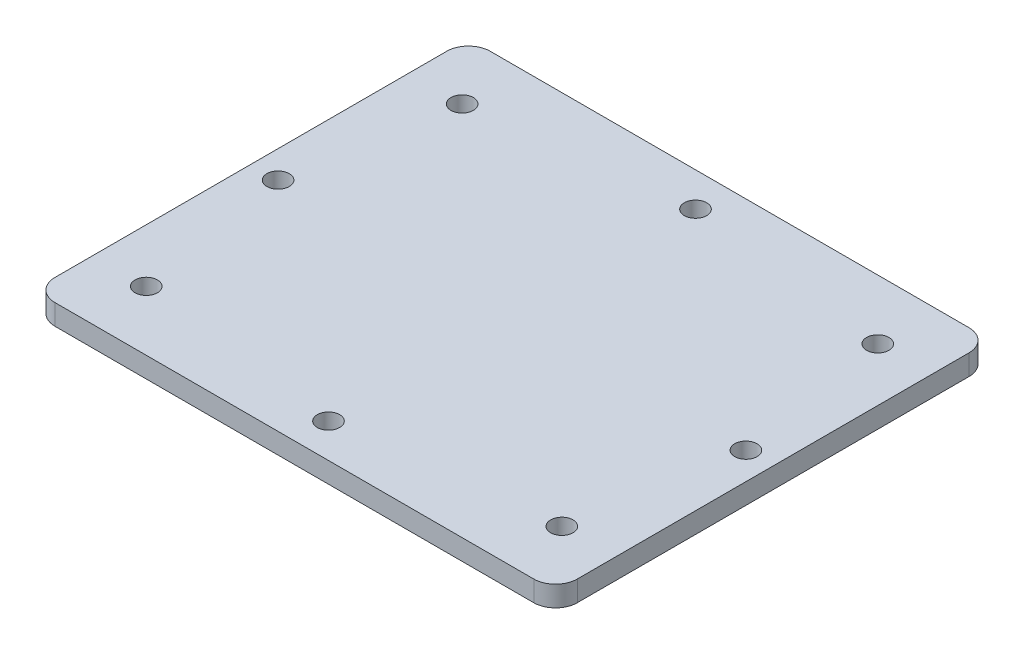
SolidWorks part; units mm, degrees
ref_plane "Front Plane" through (0, 0, 0) normal (0, 0, 1) x (1, 0, 0)
ref_plane "Top Plane" through (0, 0, 0) normal (0, 1, 0) x (1, 0, 0)
ref_plane "Right Plane" through (0, 0, 0) normal (1, 0, 0) x (0, 0, -1)
sketch "Sketch1" plane through (0, 0, 0) normal (0, 1, 0) x (1, 0, 0)
  line L0 (0, 0) -> (0, 26.77) construction
  line L5 (-38.1, 31.75) -> (38.1, 31.75)
  line L6 (-38.1, 31.75) -> (-38.1, -31.75)
  line L7 (-38.1, -31.75) -> (38.1, -31.75)
  line L8 (38.1, 31.75) -> (38.1, -31.75)
  line L9 (-38.1, 31.75) -> (38.1, -31.75) construction
  line L10 (-38.1, -31.75) -> (38.1, 31.75) construction
  line L11 (-30.315, 23.045) -> (30.315, 23.045) construction
  line L12 (-30.315, 23.045) -> (-30.315, -23.045) construction
  line L13 (-30.315, -23.045) -> (30.315, -23.045) construction
  line L14 (30.315, 23.045) -> (30.315, -23.045) construction
  line L15 (-30.315, 23.045) -> (30.315, -23.045) construction
  line L16 (-30.315, -23.045) -> (30.315, 23.045) construction
  line L17 (0, 0) -> (34.125, 0) construction
  line L18 (0, 0) -> (0, -26.77) construction
  line L19 (0, 0) -> (-34.125, 0) construction
  point P0 (0, 0)
  point P7 (0, 0)
  point P13 (-30.315, 23.045)
  point P14 (30.315, 23.045)
  point P15 (30.315, -23.045)
  point P16 (-30.315, -23.045)
  point P22 (0, 26.77)
  point P23 (-34.125, 0)
  point P24 (0, -26.77)
  point P25 (34.125, 0)
  dimension "D1" = 63.5
  dimension "D2" = 76.2
  dimension "D3" = 60.63
  dimension "D4" = 46.09
  dimension "D5" = 53.54
  dimension "D6" = 68.25
extrude "Boss-Extrude1" add sketch "Sketch1" along normal mid plane 3
fillet "Fillet1" radius 3.175 4 edges at (-38.1, 0, -31.75) (38.1, 0, -31.75) (38.1, 0, 31.75) (-38.1, 0, 31.75)
sketch "Sketch2" plane through (0, 1.5, 0) normal (0, 1, 0) x (1, 0, 0)
  point P0 (-34.125, 0)
  point P1 (-30.315, -23.045)
  point P3 (0, -26.77)
  point P5 (30.315, -23.045)
  point P7 (34.125, 0)
  point P9 (30.315, 23.045)
  point P11 (0, 26.77)
  point P13 (-30.315, 23.045)
hole_wizard "#4 Clearance Hole1" positions "Sketch2" profile "Sketch3" hole size "#4" standard "ANSI Inch"
sketch "Sketch3" plane through (-34.125, 1.5, 0) normal (1, 0, 0) x (0, 0, 1)
  line L0 (0, 0) -> (0, 7.6)
  line L1 (0, 7.6) -> (1.6319, 6.6194)
  line L2 (1.6319, 6.6194) -> (1.6319, 0)
  line L5 (1.6319, 0) -> (0, 0)
  line L10 (0, 7.6) -> (-1.632, 6.6194) construction
  line L11 (0, -6.35) -> (0, 107.95) construction
  dimension "Hole Dia." = 3.2639
  dimension "Hole Depth" = 7.6
  dimension "Drill Angle" = 118
